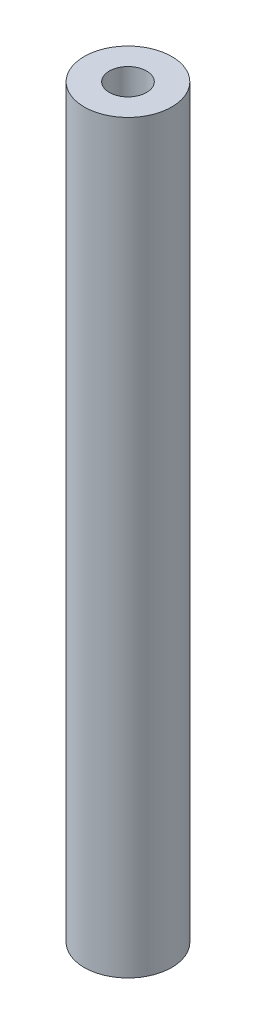
SolidWorks part; units mm, degrees
ref_plane "Front Plane" through (0, 0, 0) normal (0, 0, 1) x (1, 0, 0)
ref_plane "Top Plane" through (0, 0, 0) normal (0, 1, 0) x (1, 0, 0)
ref_plane "Right Plane" through (0, 0, 0) normal (1, 0, 0) x (0, 0, -1)
sketch "Sketch1" plane through (0, 0, 0) normal (0, 1, 0) x (1, 0, 0)
  circle A0 centre (0, 0) radius 2.055
  circle A1 centre (0, 0) radius 0.875
  dimension "D1" = 4.11
  dimension "D2" = 1.75
extrude "Boss-Extrude1" add sketch "Sketch1" along normal mid plane 35
